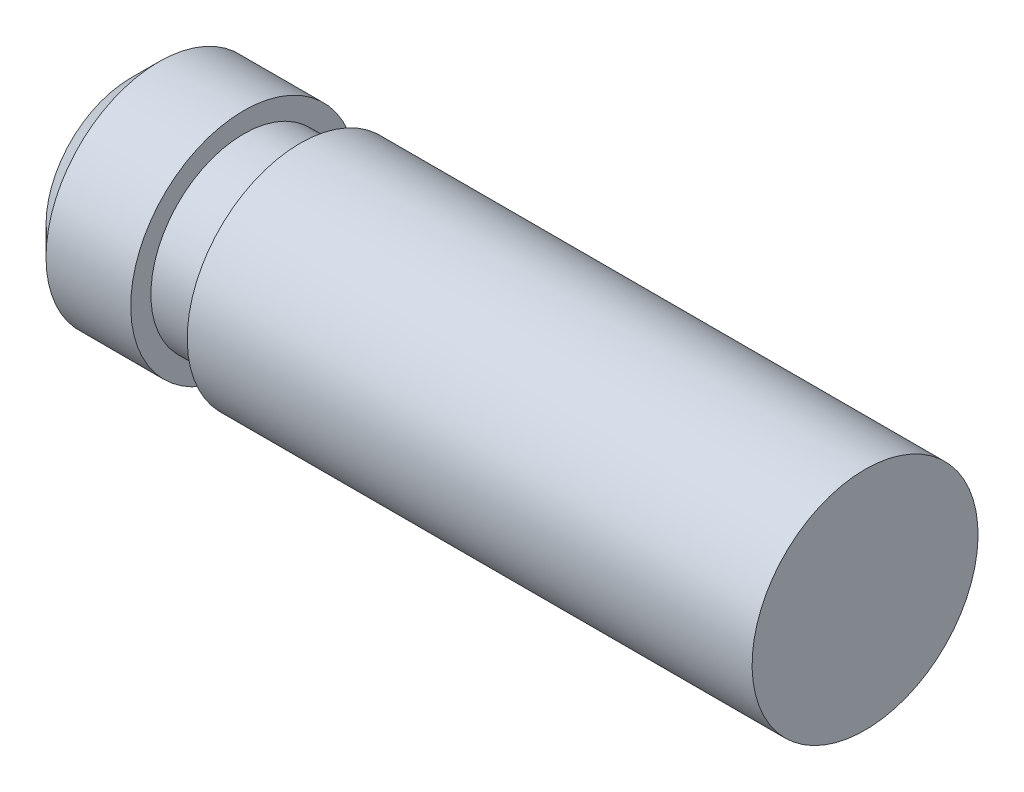
SolidWorks part; units mm, degrees
ref_plane "Front Plane" through (0, 0, 0) normal (0, 0, 1) x (1, 0, 0)
ref_plane "Top Plane" through (0, 0, 0) normal (0, 1, 0) x (1, 0, 0)
ref_plane "Right Plane" through (0, 0, 0) normal (1, 0, 0) x (0, 0, -1)
sketch "Sketch1" plane through (0, 0, 0) normal (0, 0, 1) x (1, 0, 0)
  line L0 (-4.5, 1.1815) -> (-4.5, 0.8248)
  line L1 (6.5, -0.8185) -> (-6.5, -0.8185)
  line L2 (6.5, -0.8185) -> (6.5, 1.1815)
  line L3 (6.5, 1.1815) -> (-3.5, 1.1815)
  line L4 (-6.5, -0.8185) -> (-6.5, 1.1815)
  line L5 (-4.5, 0.8248) -> (-3.5, 0.8248)
  line L6 (-3.5, 0.8248) -> (-3.5, 1.1815)
  line L7 (-4.5, 1.1815) -> (-6.5, 1.1815)
  point P0 (0, 0)
  dimension "D1" = 13
  dimension "D2" = 2
  dimension "D3" = 1
  dimension "D4" = 2
revolve "Revolve1" add sketch "Sketch1" angle 360 about L1
chamfer "Chamfer1" distance 0.5 angle 45 1 edges at (-6.5, 1.1815, 0)
